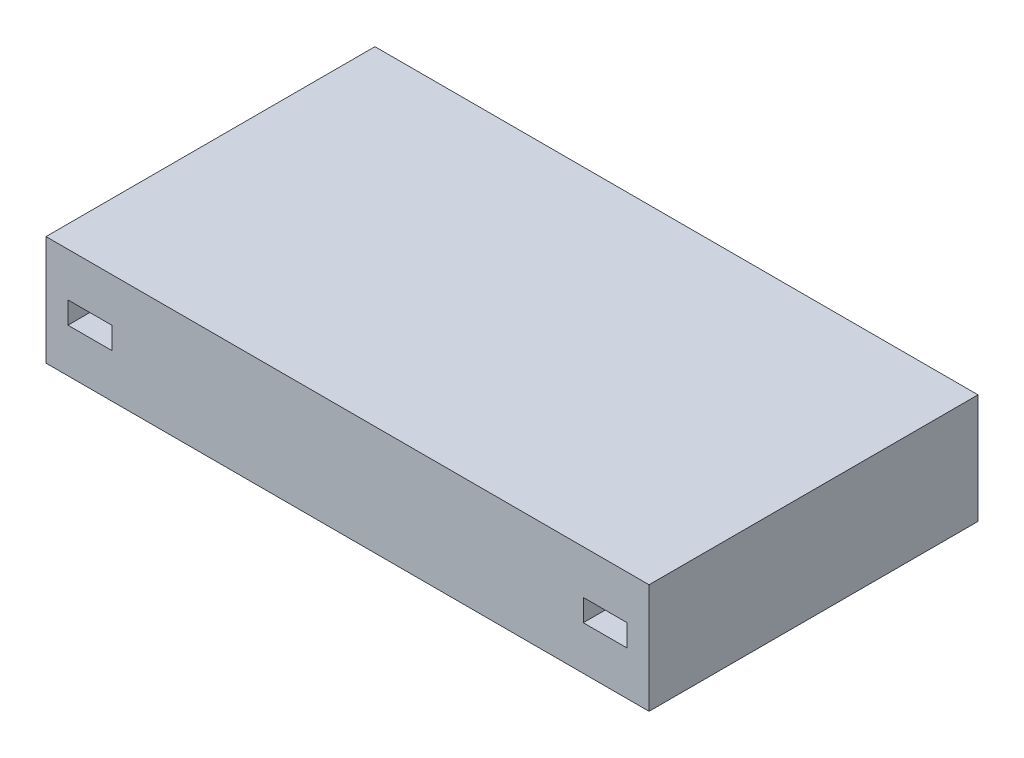
SolidWorks part; units mm, degrees
material "ABS"
ref_plane "Front Plane" through (0, 0, 0) normal (0, 0, 1) x (1, 0, 0)
ref_plane "Top Plane" through (0, 0, 0) normal (0, 1, 0) x (1, 0, 0)
ref_plane "Right Plane" through (0, 0, 0) normal (1, 0, 0) x (0, 0, -1)
sketch "Sketch1" plane through (0, 0, 0) normal (1, 0, 0) x (0, 0, -1)
  line L1 (0, 0) -> (300, 0)
  line L2 (0, 0) -> (0, 100)
  line L3 (0, 100) -> (300, 100)
  line L4 (300, 0) -> (300, 100)
  dimension "D1" = 300
  dimension "D2" = 100
extrude "Boss-Extrude1" add sketch "Sketch1" along normal blind 550
sketch "Sketch2" plane through (0, 0, 0) normal (0, 0, 1) x (1, 0, 0)
  line L0 (0, 50) -> (550, 50) construction
  line L1 (0, 100) -> (0, 0) construction
  line L2 (550, 100) -> (550, 0) construction
  line L3 (550, 100) -> (0, 100) construction
  line L4 (20, 60) -> (60, 60)
  line L5 (20, 60) -> (20, 40)
  line L6 (20, 40) -> (60, 40)
  line L7 (60, 60) -> (60, 40)
  line L12 (490, 60) -> (530, 60)
  line L13 (490, 60) -> (490, 40)
  line L14 (490, 40) -> (530, 40)
  line L15 (530, 60) -> (530, 40)
  dimension "D1" = 40
  dimension "D2" = 20
  dimension "D3" = 40
  dimension "D4" = 20
  dimension "D5" = 40
  dimension "D6" = 20
  dimension "D7" = 40
  dimension "D8" = 20
extrude "Cut-Extrude1" cut sketch "Sketch2" against normal blind 25
ref_plane "Plane1" through (0, 0, -150) normal (0, 0, 1) x (1, 0, 0)
mirror "Mirror1" about plane through (0, 0, -150) normal (0, 0, 1) of "Cut-Extrude1"
